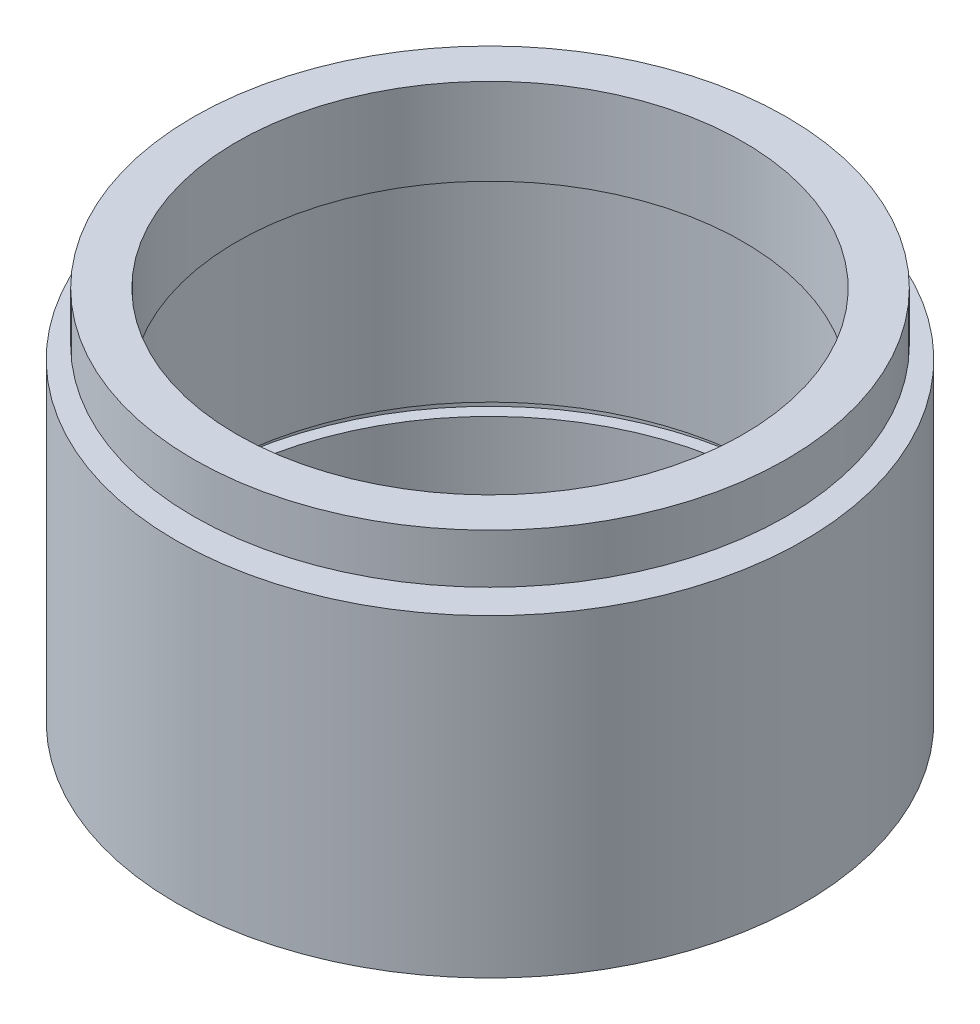
SolidWorks part; units mm, degrees
ref_plane "前视基准面" through (0, 0, 0) normal (0, 0, 1) x (1, 0, 0)
ref_plane "上视基准面" through (0, 0, 0) normal (0, 1, 0) x (1, 0, 0)
ref_plane "右视基准面" through (0, 0, 0) normal (1, 0, 0) x (0, 0, -1)
sketch "草图1" plane through (0, 0, 0) normal (0, 0, 1) x (1, 0, 0)
  line L0 (0, 161.3762) -> (0, 0) construction
  line L1 (141.7365, 0) -> (-131.7984, 0) construction
  line L2 (22.5, 22.4) -> (24, 22.4)
  line L3 (24, 22.4) -> (24, 23.4)
  line L4 (24, 23.4) -> (20.5, 23.4)
  line L5 (20.5, 23.4) -> (20.5, 30.4)
  line L6 (24, 26.4) -> (24, 30.4)
  line L7 (25.4, 25.4) -> (25.4, 0)
  line L8 (25.4, 0) -> (22.5, 0)
  line L9 (22.5, 0) -> (22.5, 5.5)
  line L10 (25.4, 25.4) -> (23.5, 25.4)
  line L11 (20.5, 30.4) -> (24, 30.4)
  line L12 (24, 26.4) -> (22.5, 26.4)
  line L13 (22.5, 26.4) -> (22.5, 25.4)
  line L14 (22.5, 6.5) -> (22.5, 22.4)
  line L15 (22.5, 5.5) -> (23.5, 5.5)
  line L16 (23.5, 5.5) -> (23.5, 6.5)
  line L17 (23.5, 6.5) -> (22.5, 6.5)
  line L18 (22.5, 25.4) -> (23.5, 25.4)
  point P10 (24.45, 25.4)
  dimension "D2" = 25.4
  dimension "D3" = 1
  dimension "D4" = 5.5
  dimension "D5" = 20.5
  dimension "D6" = 24
  dimension "D7" = 22.5
  dimension "D8" = 1
  dimension "D9" = 7
  dimension "D10" = 5
  dimension "D11" = 25.4
  dimension "D12" = 23.5
  dimension "D13" = 1
revolve "旋转1" add sketch "草图1" angle 360 about L0
cosmetic thread "装饰螺纹线1" parameters "D2"=48
cosmetic thread "装饰螺纹线2" parameters "D2"=46
cosmetic thread "装饰螺纹线3" parameters "D2"=42
cosmetic thread "装饰螺纹线5" parameters "D2"=47
